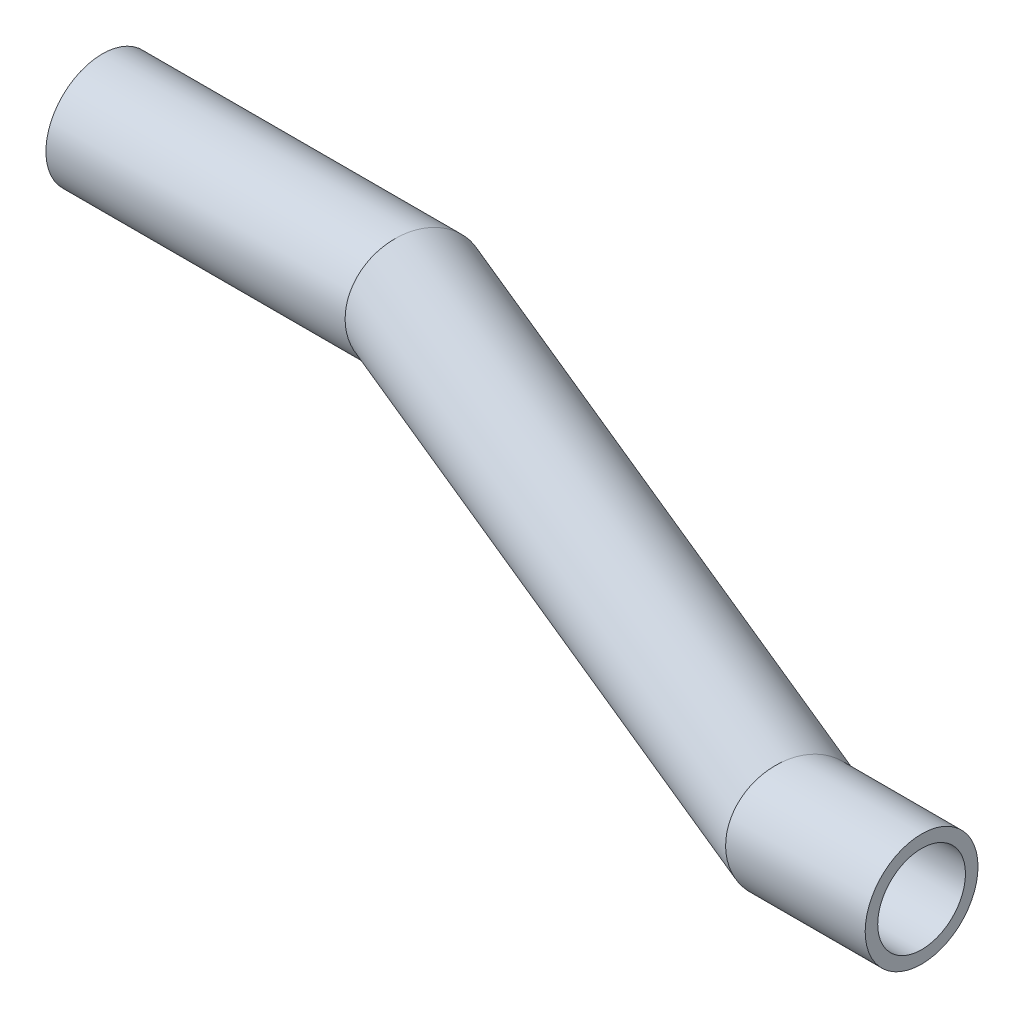
SolidWorks part; units mm, degrees
ref_plane "Front Plane" through (0, 0, 0) normal (0, 0, 1) x (1, 0, 0)
ref_plane "Top Plane" through (0, 0, 0) normal (0, 1, 0) x (1, 0, 0)
ref_plane "Right Plane" through (0, 0, 0) normal (1, 0, 0) x (0, 0, -1)
sketch3d "3DSketch1"
  line L0 (0, 0, 0) -> (65, 13.435, 34.6482)
  line L1 (0, 0, 0) -> (-25, 0, 0)
  line L2 (65, 13.435, 34.6482) -> (75, 13.435, 34.6482)
  point P0 (0, 0, 0)
  point P1 (65, 13.435, 34.6482)
  dimension "D1" = 10
  dimension "D2" = 25
sketch "Sketch2" plane through (0, 0, 0) normal (1, 0, 0) x (0, 0, -1)
  circle A0 centre (0, 0) radius 4.5
  circle A1 centre (0, 0) radius 3.5
  dimension "D1" = 9
  dimension "D2" = 7
sweep "Sweep1" add profiles "Sketch2" path "3DSketch1"
